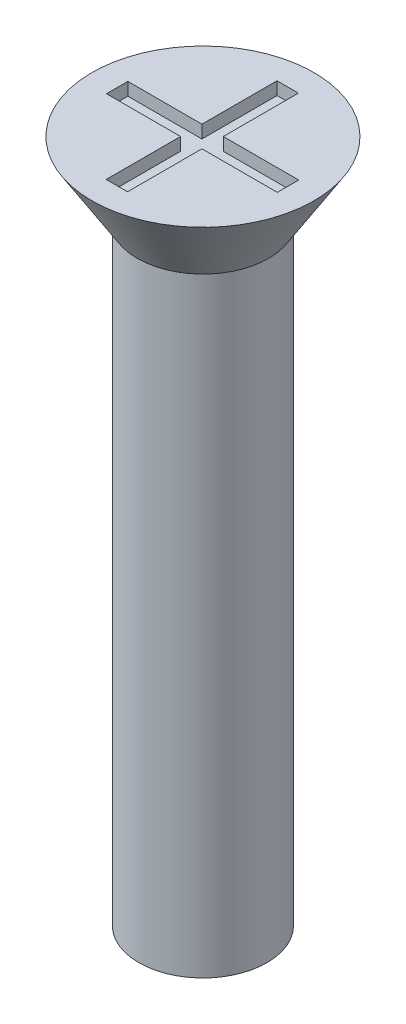
SolidWorks part; units mm, degrees
material "AISI 304"
ref_plane "Front" through (0, 0, 0) normal (0, 0, 1) x (1, 0, 0)
ref_plane "Top" through (0, 0, 0) normal (0, 1, 0) x (1, 0, 0)
ref_plane "Right" through (0, 0, 0) normal (1, 0, 0) x (0, 0, -1)
sketch "Sketch1" plane through (0, 0, 0) normal (0, 1, 0) x (1, 0, 0)
  circle A0 centre (0, 0) radius 1.5
  dimension "D1" = 3
extrude "Boss-Extrude1" add sketch "Sketch1" along normal blind 16
sketch "Sketch2" plane through (0, 16, 0) normal (0, 1, 0) x (1, 0, 0)
  circle A0 centre (0, 0) radius 2.6
  dimension "D1" = 5.2
extrude "Boss-Extrude2" add sketch "Sketch2" against normal blind 1.7 draft 32
sketch "Sketch3" plane through (0, 16, 0) normal (0, 1, 0) x (1, 0, 0)
  line L1 (-2, 0.2416) -> (2, 0.2416)
  line L2 (-2, 0.2416) -> (-2, -0.2584)
  line L3 (-2, -0.2584) -> (2, -0.2584)
  line L4 (2, 0.2416) -> (2, -0.2584)
  line L5 (-0.2653, 2) -> (0.2347, 2)
  line L6 (-0.2653, 2) -> (-0.2653, -2)
  line L7 (-0.2653, -2) -> (0.2347, -2)
  line L8 (0.2347, 2) -> (0.2347, -2)
  circle A0 centre (0, 0) radius 2.6 construction
  dimension "D1" = 0.5
  dimension "D2" = 0.5
  dimension "D3" = 4
  dimension "D4" = 4
  dimension "D5" = 2
  dimension "D6" = 2
extrude "Cut-Extrude1" cut sketch "Sketch3" against normal blind 0.3 contours L8 L5 L6 L1 | L8 L3 L6 L7 | L6 L1 L2 L3 | L1 L8 L3 L4 | L8 L1 L6 L3
